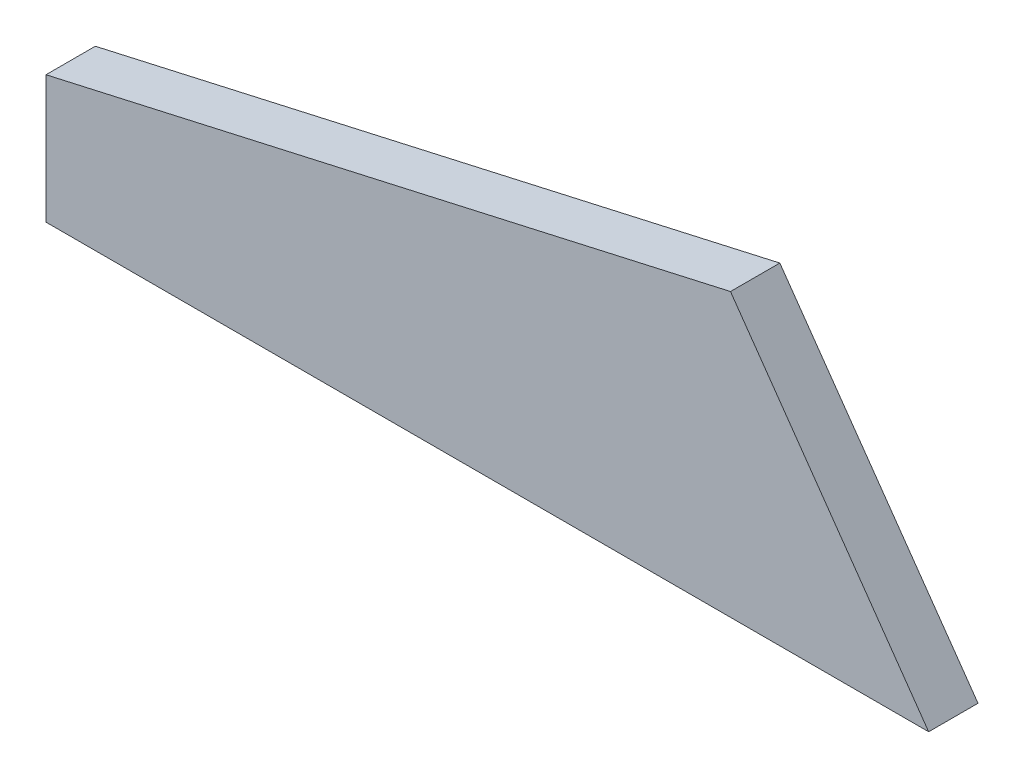
SolidWorks part; units mm, degrees
material "Erable"
ref_plane "Plan de face" through (0, 0, 0) normal (0, 0, 1) x (1, 0, 0)
ref_plane "Plan de dessus" through (0, 0, 0) normal (0, 1, 0) x (1, 0, 0)
ref_plane "Plan de droite" through (0, 0, 0) normal (1, 0, 0) x (0, 0, -1)
sketch "Esquisse1" plane through (0, 0, 0) normal (0, 0, 1) x (1, 0, 0)
  line L0 (-115, 81.0602) -> (-115, 103.0602)
  line L1 (-115, 100) -> (-115, 2) construction
  line L2 (-115, 103.0602) -> (2.9215, 129.6745)
  line L3 (2.9215, 129.6745) -> (37.062, 81.0602)
  line L4 (37.062, 81.0602) -> (-115, 81.0602)
  line L8 (45.3378, 69.2759) -> (1.4558, 131.7617) construction
  line L9 (-191.957, 85.6914) -> (4.6814, 130.0717) construction
  point P6 (12.171, 121.3339)
  point P8 (0, 133.546)
  point P9 (29.2509, 77.6716)
  point P10 (-125, 103.8548)
  dimension "D1" = 22
extrude "Boss.-Extru.1" add sketch "Esquisse1" along normal blind 8.5
